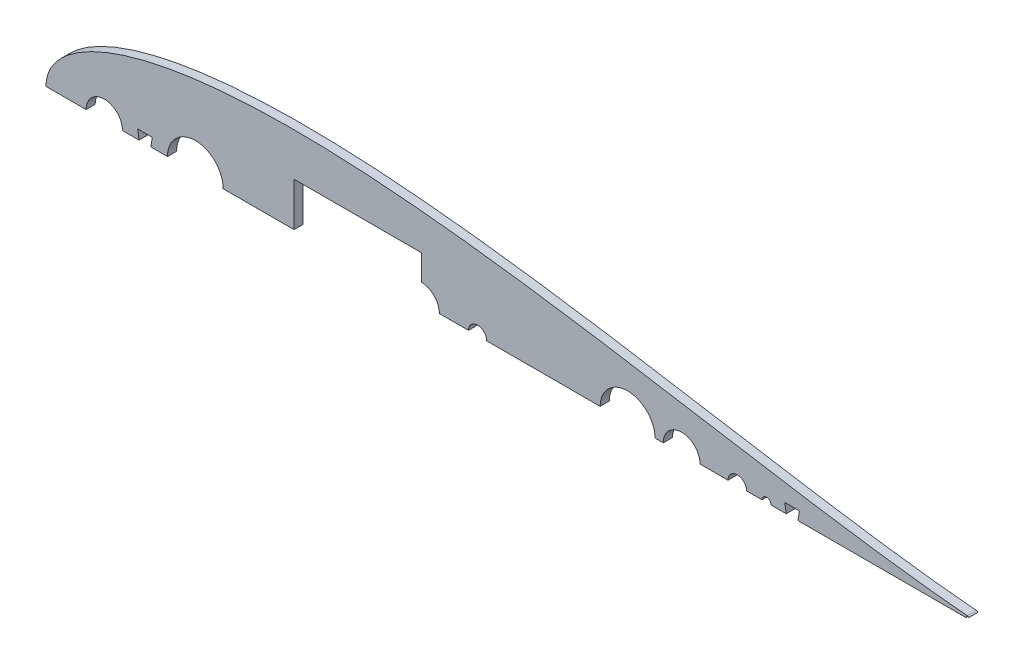
SolidWorks part; units mm, degrees
material "Beech"
ref_plane "Front Plane" through (0, 0, 0) normal (0, 0, 1) x (1, 0, 0)
ref_plane "Top Plane" through (0, 0, 0) normal (0, 1, 0) x (1, 0, 0)
ref_plane "Right Plane" through (0, 0, 0) normal (1, 0, 0) x (0, 0, -1)
curve "Curve4"
  spline degree 3 poles (100, 0, 0) (99.8498, 0.0023, 0) (99.4759, 0.008, 0) (99.1023, 0.0238, 0) (98.8789, 0.0332, 0) knots 0 0 0 0 0.401829 1 1 1 1
curve "Curve5"
  spline degree 3 poles (99.3714, -0.0082, 0) (100.2526, 0, 0) (99.3714, 0.0082, 0) (98.8504, 0.035, 0) (97.904, 0.0811, 0) (96.8285, 0.1543, 0) (95.5159, 0.2583, 0) (94.013, 0.3972, 0) (92.313, 0.574, 0) (90.4281, 0.791, 0) (88.3655, 1.0495, 0) (86.1348, 1.3497, 0) (83.7456, 1.691, 0) (81.2082, 2.0715, 0) (78.5335, 2.4886, 0) (75.7326, 2.9386, 0) (72.8172, 3.4168, 0) (69.799, 3.9177, 0) (66.6904, 4.435, 0) (63.5039, 4.9616, 0) (60.2521, 5.4899, 0) (56.948, 6.0119, 0) (53.6049, 6.519, 0) (50.2363, 7.0024, 0) (46.8558, 7.4534, 0) (43.4774, 7.8632, 0) (40.1152, 8.2232, 0) (36.7837, 8.5249, 0) (33.4975, 8.7606, 0) (30.2716, 8.923, 0) (27.1211, 9.0055, 0) (24.0614, 9.0025, 0) (21.108, 8.909, 0) (18.277, 8.7213, 0) (15.5843, 8.4369, 0) (13.0466, 8.0543, 0) (10.6806, 7.5735, 0) (8.5039, 6.996, 0) (6.5349, 6.3253, 0) (4.7933, 5.5673, 0) (3.3001, 4.7321, 0) (2.0777, 3.8366, 0) (1.1467, 2.91, 0) (0.5165, 2.0014, 0) (0.165, 1.1816, 0) (0.0231, 0.524, 0) (-0.0093, 0, 0) (0.0231, -0.524, 0) (0.165, -1.1816, 0) (0.5165, -2.0014, 0) (1.1467, -2.91, 0) (2.0777, -3.8366, 0) (3.3001, -4.7321, 0) (4.7933, -5.5673, 0) (6.5349, -6.3253, 0) (8.5039, -6.996, 0) (10.6806, -7.5735, 0) (13.0466, -8.0543, 0) (15.5843, -8.4369, 0) (18.277, -8.7213, 0) (21.108, -8.909, 0) (24.0614, -9.0025, 0) (27.1211, -9.0055, 0) (30.2716, -8.923, 0) (33.4975, -8.7606, 0) (36.7837, -8.5249, 0) (40.1152, -8.2232, 0) (43.4774, -7.8632, 0) (46.8558, -7.4534, 0) (50.2363, -7.0024, 0) (53.6049, -6.519, 0) (56.948, -6.0119, 0) (60.2521, -5.4899, 0) (63.5039, -4.9616, 0) (66.6904, -4.435, 0) (69.799, -3.9177, 0) (72.8172, -3.4168, 0) (75.7326, -2.9386, 0) (78.5335, -2.4886, 0) (81.2082, -2.0715, 0) (83.7456, -1.691, 0) (86.1348, -1.3497, 0) (88.3655, -1.0495, 0) (90.4281, -0.791, 0) (92.313, -0.574, 0) (94.013, -0.3972, 0) (95.5159, -0.2583, 0) (96.8285, -0.1543, 0) (97.904, -0.0811, 0) (98.8504, -0.035, 0) (99.3714, -0.0082, 0) (100.2526, 0, 0) (99.3714, 0.0082, 0) knots -0.009667 -0.005395 -0.002168 0 0.002168 0.005395 0.009667 0.014967 0.021271 0.028553 0.036781 0.04592 0.055932 0.066773 0.078397 0.090755 0.103793 0.117456 0.131686 0.146422 0.1616 0.177156 0.193024 0.209135 0.225421 0.241812 0.258238 0.274629 0.290914 0.307025 0.322893 0.338448 0.353626 0.368361 0.38259 0.396253 0.40929 0.421647 0.43327 0.444109 0.454119 0.463255 0.471479 0.478755 0.485052 0.490344 0.49461 0.497833 0.5 0.502167 0.50539 0.509656 0.514948 0.521245 0.528521 0.536745 0.545881 0.555891 0.56673 0.578353 0.59071 0.603747 0.61741 0.631639 0.646374 0.661552 0.677107 0.692975 0.709086 0.725371 0.741762 0.758188 0.774579 0.790865 0.806976 0.822844 0.8384 0.853578 0.868314 0.882544 0.896207 0.909245 0.921603 0.933227 0.944068 0.95408 0.963219 0.971447 0.978729 0.985033 0.990333 0.994605 0.997832 1 1.002168 1.005395 1.009667 periodic
sketch "Sketch2" plane through (0, 0, 0) normal (0, 0, 1) x (1, 0, 0)
  line L0 (100, 0) -> (0, 0) construction
  line L1 (1.2169, -991.9959) -> (1.2169, 49008.0041) construction
  line L2 (84.709, 0) -> (123.571, 0) construction
  line L3 (125.634, 0) -> (131.6629, 0) construction
  line L9 (0, 0) -> (643.9668, 0)
  line L13 (460.661, 0) -> (473.361, 0)
  circle A0 centre (104.14, 0) radius 19.431 construction
  arc A1 (1.2169, -4.6585) -> (1.2169, 4.6585) centre (9.525, 0) cw
  circle A4 centre (104.14, 0) radius 19.431
  circle A9 centre (40.64, 0) radius 12.7
  circle A14 centre (642.3793, 0) radius 1.5875 construction
  arc A15 (642.5108, -1.582) -> (642.5108, 1.582) centre (642.3793, 0) ccw
  spline S2 degree 3 poles (666.3448, -0.0547) (672.2538, 0) (666.3448, 0.0547) (662.8509, 0.2344) (656.505, 0.5436) (649.293, 1.0348) (640.4916, 1.7319) (630.4138, 2.6634) (619.0141, 3.8493) (606.375, 5.3044) (592.5439, 7.0376) (577.5855, 9.0506) (561.5643, 11.3389) (544.5497, 13.8907) (526.6141, 16.6877) (507.8326, 19.7051) (488.2827, 22.9117) (468.0444, 26.2704) (447.1994, 29.739) (425.8316, 33.2703) (404.0263, 36.8132) (381.8707, 40.3133) (359.4533, 43.7135) (336.8645, 46.9554) (314.1962, 49.9798) (291.5418, 52.7277) (268.9963, 55.1412) (246.6566, 57.1646) (224.6209, 58.7452) (202.9892, 59.8341) (181.8631, 60.3875) (161.3458, 60.367) (141.542, 59.7399) (122.5581, 58.4818) (104.5023, 56.5743) (87.485, 54.0089) (71.6197, 50.7848) (57.0237, 46.9125) (43.8205, 42.415) (32.1416, 37.3322) (22.1291, 31.7315) (13.9324, 25.7264) (7.6896, 19.5132) (3.4631, 13.4204) (1.1063, 7.9234) (0.1546, 3.5138) (-0.0622, 0) (0.1546, -3.5138) (1.1063, -7.9234) (3.4631, -13.4204) (7.6896, -19.5132) (13.9324, -25.7264) (22.1291, -31.7315) (32.1416, -37.3322) (43.8205, -42.415) (57.0237, -46.9125) (71.6197, -50.7848) (87.485, -54.0089) (104.5023, -56.5743) (122.5581, -58.4818) (141.542, -59.7399) (161.3458, -60.367) (181.8631, -60.3875) (202.9892, -59.8341) (224.6209, -58.7452) (246.6566, -57.1646) (268.9963, -55.1412) (291.5418, -52.7277) (314.1962, -49.9798) (336.8645, -46.9554) (359.4533, -43.7135) (381.8707, -40.3133) (404.0263, -36.8132) (425.8316, -33.2703) (447.1994, -29.739) (468.0444, -26.2704) (488.2827, -22.9117) (507.8326, -19.7051) (526.6141, -16.6877) (544.5497, -13.8907) (561.5643, -11.3389) (577.5855, -9.0506) (592.5439, -7.0376) (606.375, -5.3044) (619.0141, -3.8493) (630.4138, -2.6634) (640.4916, -1.7319) (649.293, -1.0348) (656.505, -0.5436) (662.8509, -0.2344) (666.3448, -0.0547) (672.2538, 0) (666.3448, 0.0547) knots -0.009667 -0.005395 -0.002168 0 0.002168 0.005395 0.009667 0.014967 0.021271 0.028553 0.036781 0.04592 0.055932 0.066773 0.078397 0.090755 0.103793 0.117456 0.131686 0.146422 0.1616 0.177156 0.193024 0.209135 0.225421 0.241812 0.258238 0.274629 0.290914 0.307025 0.322893 0.338448 0.353626 0.368361 0.38259 0.396253 0.40929 0.421647 0.43327 0.444109 0.454119 0.463255 0.471479 0.478755 0.485052 0.490344 0.49461 0.497833 0.5 0.502167 0.50539 0.509656 0.514948 0.521245 0.528521 0.536745 0.545881 0.555891 0.56673 0.578353 0.59071 0.603747 0.61741 0.631639 0.646374 0.661552 0.677107 0.692975 0.709086 0.725371 0.741762 0.758188 0.774579 0.790865 0.806976 0.822844 0.8384 0.853578 0.868314 0.882544 0.896207 0.909245 0.921603 0.933227 0.944068 0.95408 0.963219 0.971447 0.978729 0.985033 0.990333 0.994605 0.997832 1 1.002168 1.005395 1.009667 only from (670.56, 0) to (670.56, 0)
  point P2 (167.64, 0)
  point P8 (1.2169, -4.6585)
  point P10 (1.2169, 4.6585)
  point P28 (133.9182, 0)
  point P49 (130.0977, 0)
  point P59 (95.1064, 0)
  dimension "D2" = 38.862
  dimension "D8" = 25.4
  dimension "D9" = 63.5
  dimension "D10" = 3.175
  dimension "D1" = 167.64
  dimension "D6" = 63.5
extrude "Boss-Extrude1" add sketch "Sketch2" along normal blind 6.35
sketch "Sketch3" plane through (0, 0, 6.35) normal (0, 0, 1) x (1, 0, 0)
  line L0 (123.571, 0) -> (643.9668, 0) construction
  line L1 (221.3683, -1074.4001) -> (221.3683, 48925.5999) construction
  line L2 (135.001, -1074.4001) -> (135.001, 48925.5999) construction
  line L3 (307.8396, -1010.7759) -> (307.8396, 48989.2241) construction
  line L4 (232.7983, -1029.5884) -> (232.7983, 48970.4116) construction
  line L5 (319.2696, -1040.0065) -> (319.2696, 48959.9935) construction
  line L6 (374.9948, -1040.8965) -> (374.9948, 48959.1035) construction
  line L7 (386.4248, -1038.9384) -> (386.4248, 48961.0616) construction
  line L8 (424.7788, -1033.2699) -> (424.7788, 48966.7301) construction
  circle A0 centre (178.1847, 0) radius 43.1837
  circle A1 centre (270.319, 0) radius 37.5206
  circle A2 centre (347.1322, 0) radius 27.8626
  circle A3 centre (405.6018, -0.2463) radius 19.177
  circle A4 centre (443.3019, 0) radius 12.827
  circle A5 centre (482.0825, 0) radius 6.477
  circle A6 centre (502.475, 0) radius 3.175
  circle A7 centre (300.99, 0) radius 6.35
  arc A8 (123.571, 0) -> (84.709, 0) centre (104.14, 0) ccw construction
  circle A9 centre (261.62, 0) radius 12.7
  spline S0 degree 3 poles (666.3448, -0.0547) (672.2538, 0) (666.3448, 0.0547) (662.8509, 0.2344) (656.505, 0.5436) (649.293, 1.0348) (640.4916, 1.7319) (630.4138, 2.6634) (619.0141, 3.8493) (606.375, 5.3044) (592.5439, 7.0376) (577.5855, 9.0506) (561.5643, 11.3389) (544.5497, 13.8907) (526.6141, 16.6877) (507.8326, 19.7051) (488.2827, 22.9117) (468.0444, 26.2704) (447.1994, 29.739) (425.8316, 33.2703) (404.0263, 36.8132) (381.8707, 40.3133) (359.4533, 43.7135) (336.8645, 46.9554) (314.1962, 49.9798) (291.5418, 52.7277) (268.9963, 55.1412) (246.6566, 57.1646) (224.6209, 58.7452) (202.9892, 59.8341) (181.8631, 60.3875) (161.3458, 60.367) (141.542, 59.7399) (122.5581, 58.4818) (104.5023, 56.5743) (87.485, 54.0089) (71.6197, 50.7848) (57.0237, 46.9125) (43.8205, 42.415) (32.1416, 37.3322) (22.1291, 31.7315) (13.9324, 25.7264) (7.6896, 19.5132) (3.4631, 13.4204) (1.1063, 7.9234) (0.1546, 3.5138) (-0.0622, 0) (0.1546, -3.5138) (1.1063, -7.9234) (3.4631, -13.4204) (7.6896, -19.5132) (13.9324, -25.7264) (22.1291, -31.7315) (32.1416, -37.3322) (43.8205, -42.415) (57.0237, -46.9125) (71.6197, -50.7848) (87.485, -54.0089) (104.5023, -56.5743) (122.5581, -58.4818) (141.542, -59.7399) (161.3458, -60.367) (181.8631, -60.3875) (202.9892, -59.8341) (224.6209, -58.7452) (246.6566, -57.1646) (268.9963, -55.1412) (291.5418, -52.7277) (314.1962, -49.9798) (336.8645, -46.9554) (359.4533, -43.7135) (381.8707, -40.3133) (404.0263, -36.8132) (425.8316, -33.2703) (447.1994, -29.739) (468.0444, -26.2704) (488.2827, -22.9117) (507.8326, -19.7051) (526.6141, -16.6877) (544.5497, -13.8907) (561.5643, -11.3389) (577.5855, -9.0506) (592.5439, -7.0376) (606.375, -5.3044) (619.0141, -3.8493) (630.4138, -2.6634) (640.4916, -1.7319) (649.293, -1.0348) (656.505, -0.5436) (662.8509, -0.2344) (666.3448, -0.0547) (672.2538, 0) (666.3448, 0.0547) knots -0.009667 -0.005395 -0.002168 0 0.002168 0.005395 0.009667 0.014967 0.021271 0.028553 0.036781 0.04592 0.055932 0.066773 0.078397 0.090755 0.103793 0.117456 0.131686 0.146422 0.1616 0.177156 0.193024 0.209135 0.225421 0.241812 0.258238 0.274629 0.290914 0.307025 0.322893 0.338448 0.353626 0.368361 0.38259 0.396253 0.40929 0.421647 0.43327 0.444109 0.454119 0.463255 0.471479 0.478755 0.485052 0.490344 0.49461 0.497833 0.5 0.502167 0.50539 0.509656 0.514948 0.521245 0.528521 0.536745 0.545881 0.555891 0.56673 0.578353 0.59071 0.603747 0.61741 0.631639 0.646374 0.661552 0.677107 0.692975 0.709086 0.725371 0.741762 0.758188 0.774579 0.790865 0.806976 0.822844 0.8384 0.853578 0.868314 0.882544 0.896207 0.909245 0.921603 0.933227 0.944068 0.95408 0.963219 0.971447 0.978729 0.985033 0.990333 0.994605 0.997832 1 1.002168 1.005395 1.009667 only from (642.5108, 1.582) to (0, 0) construction
  spline S1 degree 3 poles (642.5108, 1.582) (641.9934, 1.6251) (638.0937, 1.9535) (630.4138, 2.6634) (619.0141, 3.8493) (606.375, 5.3044) (592.5439, 7.0376) (577.5855, 9.0506) (561.5643, 11.3389) (544.5497, 13.8907) (526.6141, 16.6877) (507.8326, 19.7051) (488.2827, 22.9117) (468.0444, 26.2704) (447.1994, 29.739) (425.8316, 33.2703) (404.0263, 36.8132) (381.8707, 40.3133) (359.4533, 43.7135) (336.8645, 46.9554) (314.1962, 49.9798) (291.5418, 52.7277) (268.9963, 55.1412) (246.6566, 57.1646) (224.6209, 58.7452) (202.9892, 59.8341) (181.8631, 60.3875) (161.3458, 60.367) (141.542, 59.7399) (122.5581, 58.4818) (104.5023, 56.5743) (87.485, 54.0089) (71.6197, 50.7848) (57.0237, 46.9125) (43.8205, 42.415) (32.1416, 37.3322) (22.1291, 31.7315) (13.9324, 25.7264) (7.6896, 19.5132) (3.4631, 13.4204) (1.1063, 7.9234) (0.1546, 3.5138) (0, 1.0075) (0, 0) knots 0.020157 0.020157 0.020157 0.020157 0.021271 0.028553 0.036781 0.04592 0.055932 0.066773 0.078397 0.090755 0.103793 0.117456 0.131686 0.146422 0.1616 0.177156 0.193024 0.209135 0.225421 0.241812 0.258238 0.274629 0.290914 0.307025 0.322893 0.338448 0.353626 0.368361 0.38259 0.396253 0.40929 0.421647 0.43327 0.444109 0.454119 0.463255 0.471479 0.478755 0.485052 0.490344 0.49461 0.497833 0.5 0.5 0.5 0.5
  spline S2 degree 1 poles (641.09, -15.504) (17.145, 0) knots 0 0 1 1 construction
  spline S3 degree 3 poles (641.09, -15.504) (639.3109, -15.356) (635.7469, -15.0465) (628.6795, -14.3848) (616.3376, -13.1228) (598.7968, -11.07) (577.8544, -8.3122) (550.0407, -4.3344) (526.7675, -0.7058) (507.1428, 2.4564) (499.6739, 3.672) (493.0571, 4.7561) (486.443, 5.8439) (479.833, 6.9363) (468.6627, 8.7879) (454.6679, 11.1162) (439.2724, 13.6723) (427.0242, 15.6918) (414.7804, 17.6976) (402.5424, 19.6775) (383.7341, 22.6657) (364.1941, 25.6789) (337.2548, 29.6013) (311.6033, 33.0557) (285.956, 36.1082) (258.5568, 38.96) (226.6306, 41.5901) (199.8846, 42.824) (181.9553, 43.1587) (174.3292, 43.2245) (161.617, 43.1735) (145.5526, 42.7712) (125.352, 41.5355) (105.3611, 39.4431) (85.7017, 36.3258) (69.7697, 32.6872) (57.4923, 28.9971) (48.6128, 25.7921) (40.1947, 22.1041) (32.4382, 17.8906) (25.6768, 13.1616) (21.3298, 8.9237) (18.9766, 5.6746) (17.8297, 3.4581) (17.3476, 1.8975) (17.1726, 0.7891) (17.145, 0.266) (17.145, 0) knots 0.020157 0.020157 0.020157 0.020157 0.023906 0.027655 0.035152 0.050147 0.065142 0.080137 0.110128 0.11557 0.122767 0.126366 0.129965 0.137163 0.140761 0.154305 0.167682 0.174371 0.181059 0.194437 0.201125 0.222192 0.237187 0.260079 0.278331 0.293326 0.320059 0.348251 0.352 0.359498 0.365044 0.380039 0.395034 0.410029 0.425025 0.44002 0.447517 0.455015 0.462512 0.47001 0.477507 0.485005 0.488754 0.492502 0.496251 0.498126 0.5 0.5 0.5 0.5 construction
  line M15 (123.571, 0) -> (643.9668, 0)
  dimension "D6" = 38.354
  dimension "D7" = 25.654
  dimension "D8" = 12.954
  dimension "D9" = 6.35
  dimension "D10" = 12.7
  dimension "D12" = 25.4
  dimension "D2" = 11.43
  dimension "D3" = 11.43
  dimension "D4" = 11.43
  dimension "D5" = 11.43
  dimension "D11" = 196.85
  dimension "D13" = 157.48
  dimension "D1" = 17.145
extrude "Cut-Extrude1" cut sketch "Sketch3" against normal through all both and the other way through all contours A3 M15 | A4 M15 | A5 M15 | A6 M15 | A9 M15 | A7 M15
sketch "Sketch4" plane through (0, 0, 6.35) normal (0, 0, 1) x (1, 0, 0)
  line L0 (53.34, 0) -> (84.709, 0) construction
  line L1 (53.34, 0) -> (84.709, 0)
  line L2 (63.9445, 6.35) -> (74.1045, 6.35)
  line L3 (65.8495, 6.35) -> (72.1995, 6.35)
  line L4 (65.8495, 6.35) -> (65.8495, -6.35)
  line L5 (65.8495, -6.35) -> (72.1995, -6.35)
  line L6 (72.1995, 6.35) -> (72.1995, -6.35)
  line L7 (65.8495, 6.35) -> (72.1995, -6.35) construction
  line L8 (65.8495, -6.35) -> (72.1995, 6.35) construction
  line L9 (63.9445, 6.35) -> (65.8495, -6.35)
  line L10 (72.1995, -6.35) -> (74.1045, 6.35)
  line L11 (488.5595, 0) -> (499.3, 0) construction
  line L12 (517.1345, 6.35) -> (523.4845, 6.35)
  line L13 (517.1345, 6.35) -> (517.1345, -6.35)
  line L14 (517.1345, -6.35) -> (523.4845, -6.35)
  line L15 (523.4845, 6.35) -> (523.4845, -6.35)
  line L16 (517.1345, 6.35) -> (523.4845, -6.35) construction
  line L17 (517.1345, -6.35) -> (523.4845, 6.35) construction
  line L18 (515.2295, 6.35) -> (525.3895, 6.35)
  line L19 (517.1345, -6.35) -> (515.2295, 6.35)
  line L20 (523.4845, -6.35) -> (525.3895, 6.35)
  point P2 (69.0245, 0)
  point P9 (69.0245, 6.35)
  point P10 (69.0245, 6.35)
  point P11 (52.0538, -5.8748)
  point P12 (520.3095, 0)
  point P21 (520.3095, 6.35)
  point P22 (520.3095, 6.35)
  line M18 (488.5595, 0) -> (499.3, 0)
  line M23 (53.34, 0) -> (84.709, 0)
  dimension "D1" = 12.7
  dimension "D2" = 6.35
  dimension "D3" = 10.16
  dimension "D4" = 6.35
  dimension "D5" = 12.7
  dimension "D6" = 31.75
  dimension "D7" = 10.16
extrude "Cut-Extrude2" cut sketch "Sketch4" against normal blind 6.35 contours L19 L13 L18 M18 | L15 L12 L13 M18 | L20 L18 L15 M18 | L2 L9 L1 L4 | L6 L2 L4 L1 | L10 L2 L6 M23
sketch "Sketch5" plane through (0, 0, 6.35) normal (0, 0, 1) x (1, 0, 0)
  text T0 "Servo Access Airfoil" font "Century Gothic" height 5.08
extrude "Cut-Extrude4" cut sketch "Sketch7" against normal through all
sketch "Sketch7" plane through (327.9592, -13.7514, 6.35) normal (0, 0, 1) x (1, 0, 0)
  line L1 (-154.9852, -16.7286) -> (-66.0852, -16.7286)
  line L2 (-154.9852, -16.7286) -> (-154.9852, 44.2314)
  line L3 (-154.9852, 44.2314) -> (-66.0852, 44.2314)
  line L4 (-66.0852, -16.7286) -> (-66.0852, 44.2314)
  line L5 (-154.9852, -16.7286) -> (-66.0852, 44.2314) construction
  line L6 (-154.9852, 44.2314) -> (-66.0852, -16.7286) construction
  point P0 (-110.5352, 13.7514)
extrude "Cut-Extrude5" cut sketch "Sketch8" against normal through all
sketch "Sketch8" plane through (327.9592, -13.7514, 6.35) normal (0, 0, 1) x (1, 0, 0)
  circle A0 centre (314.9285, 13.7514) radius 1.2446
equation "\"0.5n\"=0"
